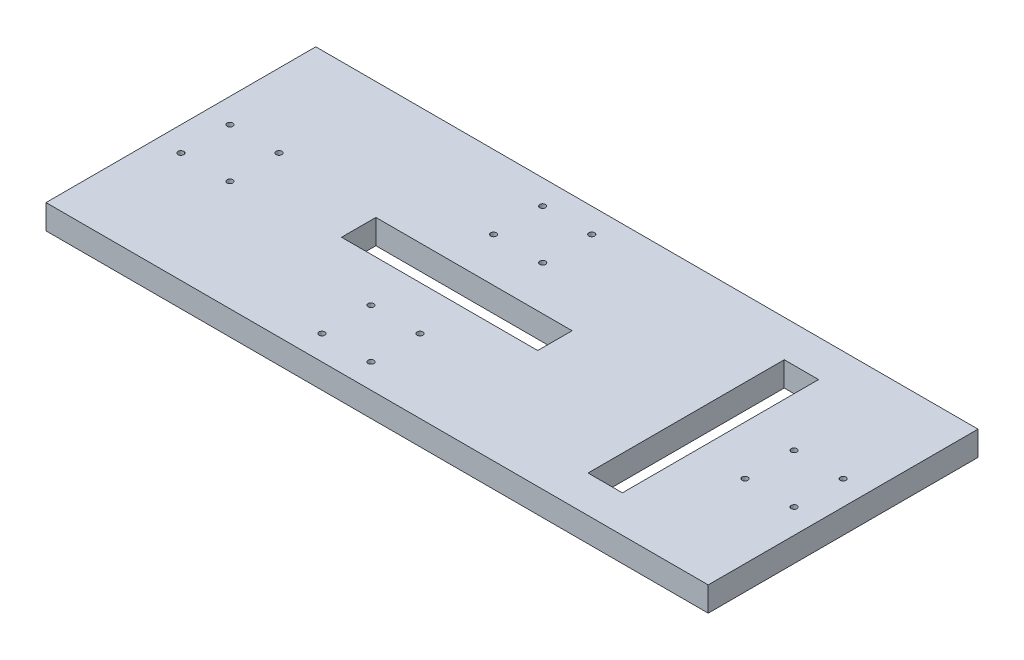
SolidWorks part; units mm, degrees
ref_plane "Front Plane" through (0, 0, 0) normal (0, 0, 1) x (1, 0, 0)
ref_plane "Top Plane" through (0, 0, 0) normal (0, 1, 0) x (1, 0, 0)
ref_plane "Right Plane" through (0, 0, 0) normal (1, 0, 0) x (0, 0, -1)
sketch "Sketch1" plane through (0, 0, 0) normal (0, 1, 0) x (1, 0, 0)
  line L1 (0, 0) -> (342.9, 0)
  line L2 (0, 0) -> (0, 139.7)
  line L3 (0, 139.7) -> (342.9, 139.7)
  line L4 (342.9, 0) -> (342.9, 139.7)
  dimension "D1" = 139.7
  dimension "D2" = 342.9
extrude "Boss-Extrude1" add sketch "Sketch1" along normal blind 12.7
sketch "Sketch3" plane through (0, 12.7, 0) normal (0, 1, 0) x (1, 0, 0)
  line L0 (171.45, 139.7) -> (171.45, -49860.3) construction
  line L1 (342.9, 139.7) -> (0, 139.7) construction
  line L2 (0, 0) -> (342.9, 0) construction
  line L3 (342.9, 69.85) -> (-49657.1, 69.85) construction
  line L4 (342.9, 0) -> (342.9, 139.7) construction
  line L5 (0, 139.7) -> (0, 0) construction
  line L11 (304.8, 82.55) -> (330.2, 82.55) construction
  line L12 (304.8, 82.55) -> (304.8, 57.15) construction
  line L13 (304.8, 57.15) -> (330.2, 57.15) construction
  line L14 (330.2, 82.55) -> (330.2, 57.15) construction
  circle A4 centre (330.2, 82.55) radius 1.5
  circle A5 centre (330.2, 57.15) radius 1.5
  circle A6 centre (304.8, 57.15) radius 1.5
  circle A7 centre (304.8, 82.55) radius 1.5
  point P4 (171.45, 139.7)
  point P7 (171.45, 0)
  point P12 (342.9, 69.85)
  point P15 (0, 69.85)
  point P25 (304.8, 69.85)
  dimension "D11" = 3
  dimension "D12" = 3
  dimension "D13" = 3
  dimension "D14" = 3
  dimension "D4" = 25.4
  dimension "D5" = 25.4
  dimension "D6" = 12.7
extrude "Cut-Extrude1" cut sketch "Sketch3" against normal through all
ref_plane "Plane1" through (171.45, 0, 0) normal (-1, 0, 0) x (0, 0, 1)
ref_plane "Plane2" through (0, 0, -69.85) normal (0, 0, -1) x (-1, 0, 0)
mirror "Mirror1" about plane through (171.45, 0, 0) normal (-1, 0, 0) of "Cut-Extrude1"
sketch "Sketch4" plane through (0, 12.7, 0) normal (0, 1, 0) x (1, 0, 0)
  line L0 (6.985, 69.85) -> (-6.985, 69.85) construction
  line L1 (261.62, 120.65) -> (279.4, 120.65)
  line L2 (261.62, 120.65) -> (261.62, 19.05)
  line L3 (261.62, 19.05) -> (279.4, 19.05)
  line L4 (279.4, 120.65) -> (279.4, 19.05)
  line L5 (342.9, 0) -> (342.9, 139.7) construction
  line L7 (92.075, 78.74) -> (193.675, 78.74)
  line L8 (92.075, 78.74) -> (92.075, 60.96)
  line L9 (92.075, 60.96) -> (193.675, 60.96)
  line L10 (193.675, 78.74) -> (193.675, 60.96)
  line L12 (171.45, 6.985) -> (171.45, -6.985) construction
  point P4 (279.4, 69.85)
  point P13 (92.075, 69.85)
  point P14 (142.875, 78.74)
  dimension "D1" = 17.78
  dimension "D2" = 101.6
  dimension "D3" = 63.5
  dimension "D4" = 101.6
  dimension "D5" = 17.78
  dimension "D6" = 28.575
extrude "Cut-Extrude2" cut sketch "Sketch4" against normal through all
sketch "Sketch5" plane through (0, 12.7, 0) normal (0, 1, 0) x (1, 0, 0)
  line L0 (342.9, 139.7) -> (0, 139.7) construction
  line L1 (130.175, 127) -> (155.575, 127) construction
  line L2 (130.175, 127) -> (130.175, 101.6) construction
  line L3 (130.175, 101.6) -> (155.575, 101.6) construction
  line L4 (155.575, 127) -> (155.575, 101.6) construction
  line L5 (171.45, 6.985) -> (171.45, -6.985) construction
  circle A0 centre (130.175, 127) radius 1.5
  circle A1 centre (155.575, 127) radius 1.5
  circle A2 centre (155.575, 101.6) radius 1.5
  circle A3 centre (130.175, 101.6) radius 1.5
  dimension "D5" = 3
  dimension "D6" = 3
  dimension "D7" = 3
  dimension "D8" = 3
  dimension "D1" = 12.7
  dimension "D2" = 25.4
  dimension "D3" = 25.4
  dimension "D4" = 15.875
extrude "Cut-Extrude3" cut sketch "Sketch5" against normal through all
mirror "Mirror3" about plane through (0, 0, -69.85) normal (0, 0, -1) of "Cut-Extrude3"
